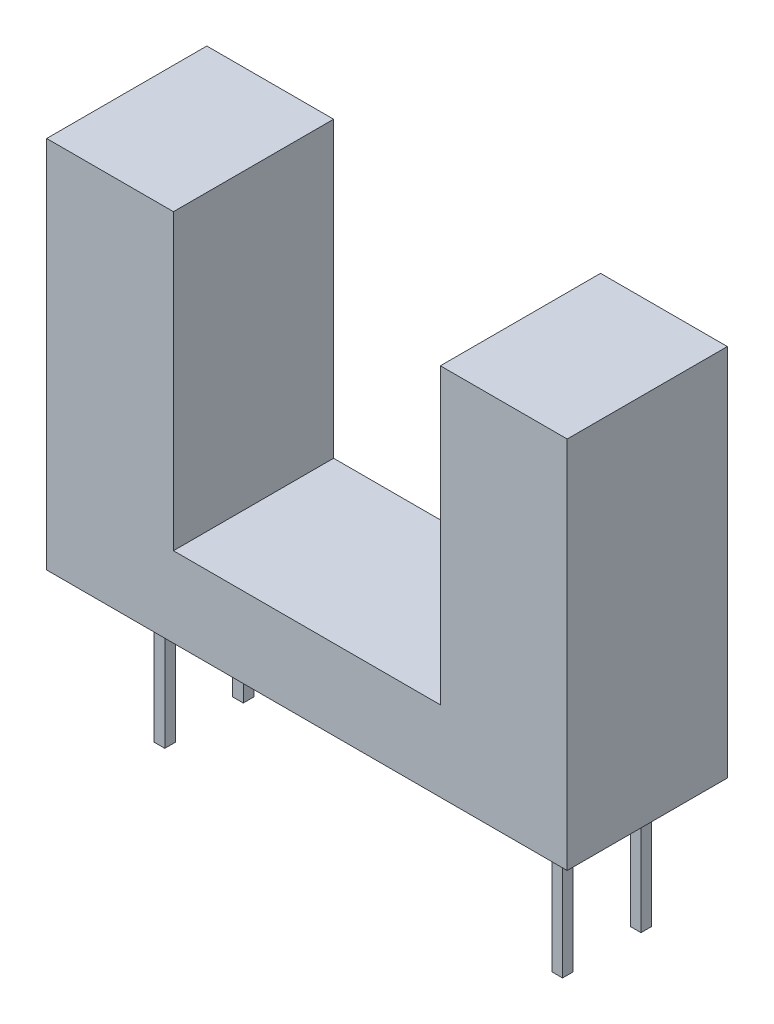
SolidWorks part; units mm, degrees
material "ABS"
ref_plane "Front Plane" through (0, 0, 0) normal (0, 0, 1) x (1, 0, 0)
ref_plane "Top Plane" through (0, 0, 0) normal (0, 1, 0) x (1, 0, 0)
ref_plane "Right Plane" through (0, 0, 0) normal (1, 0, 0) x (0, 0, -1)
sketch "Sketch1" plane through (0, 0, 0) normal (0, 0, 1) x (1, 0, 0)
  line L0 (0, 10.392) -> (0, -11.0789) construction
  line L1 (-17.111, 0) -> (15.2297, 0) construction
  line L2 (-5, 7) -> (-5, -4)
  line L3 (-9.75, 7) -> (-5, 7)
  line L4 (-9.75, 7) -> (-9.75, -7)
  line L5 (-9.75, -7) -> (9.75, -7)
  line L6 (9.75, 7) -> (9.75, -7)
  line L7 (5, 7) -> (5, -4)
  line L8 (-5, -4) -> (5, -4)
  line L9 (5, 7) -> (9.75, 7)
  point P9 (-5, 7)
  dimension "D1" = 19.5
  dimension "D2" = 14
  dimension "D3" = 9.75
  dimension "D4" = 7
  dimension "D5" = 10
  dimension "D6" = 11
extrude "Boss-Extrude1" add sketch "Sketch1" along normal blind 6 contours L2 L8 L7 L9 L6 L5 L4 L3
sketch "Sketch2" plane through (0, -7, 0) normal (0, -1, 0) x (1, 0, 0)
  line L0 (0, 8.2757) -> (0, -3.1087) construction
  line L1 (-12.9115, 2.5835) -> (13.1495, 2.5835) construction
  line L3 (-7.65, 4.0743) -> (-7.25, 4.0743)
  line L4 (-7.65, 4.0743) -> (-7.65, 3.6743)
  line L5 (-7.65, 3.6743) -> (-7.25, 3.6743)
  line L6 (-7.25, 4.0743) -> (-7.25, 3.6743)
  line L16 (7.25, 4.0743) -> (7.25, 3.6743)
  line L17 (7.65, 3.6743) -> (7.25, 3.6743)
  line L18 (7.65, 4.0743) -> (7.65, 3.6743)
  line L19 (7.65, 4.0743) -> (7.25, 4.0743)
  line L20 (7.25, 1.1343) -> (7.25, 0.7343)
  line L21 (-7.65, 1.1343) -> (-7.25, 1.1343)
  line L22 (-7.65, 1.1343) -> (-7.65, 0.7343)
  line L23 (-7.65, 0.7343) -> (-7.25, 0.7343)
  line L24 (-7.25, 1.1343) -> (-7.25, 0.7343)
  line L25 (7.65, 0.7343) -> (7.25, 0.7343)
  line L26 (7.65, 1.1343) -> (7.65, 0.7343)
  line L27 (7.65, 1.1343) -> (7.25, 1.1343)
  dimension "D1" = 0.4
  dimension "D2" = 14.5
  dimension "D3" = 0.4
  dimension "D4" = 0.4
  dimension "D5" = 0.4
  dimension "D6" = 2.54
  dimension "D7" = 14.5
extrude "Boss-Extrude2" add sketch "Sketch2" along normal blind 5.5
